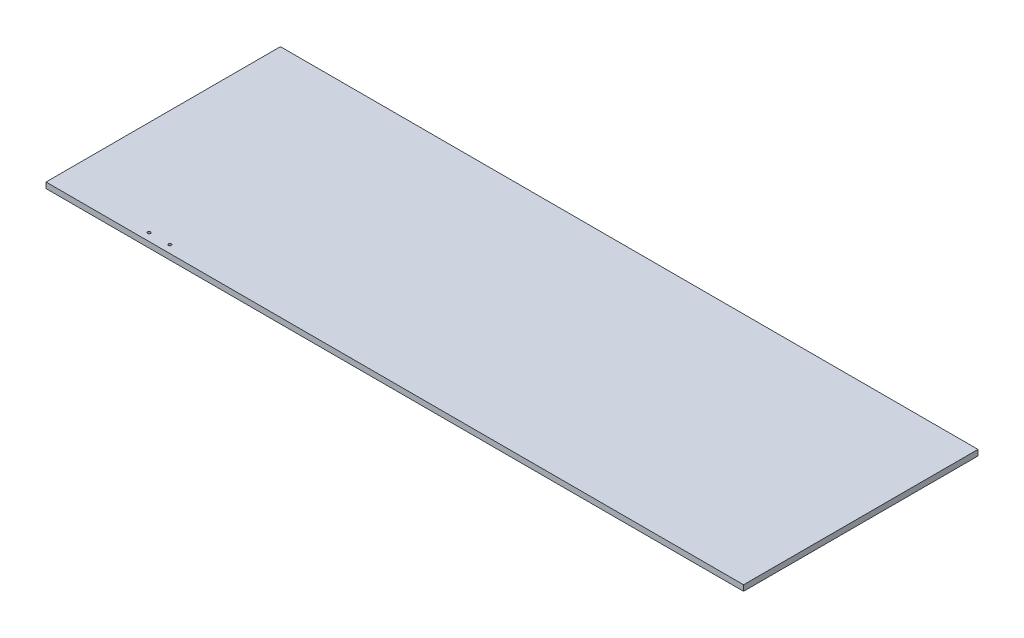
SolidWorks part; units mm, degrees
material "Oak"
ref_plane "Front Plane" through (0, 0, 0) normal (0, 0, 1) x (1, 0, 0)
ref_plane "Top Plane" through (0, 0, 0) normal (0, 1, 0) x (1, 0, 0)
ref_plane "Right Plane" through (0, 0, 0) normal (1, 0, 0) x (0, 0, -1)
sketch "Sketch1" plane through (0, 0, 0) normal (0, 1, 0) x (1, 0, 0)
  line L1 (0, 410) -> (1220, 410)
  line L2 (0, 410) -> (0, 0)
  line L3 (0, 0) -> (1220, 0)
  line L4 (1220, 410) -> (1220, 0)
  point P4 (0, 0)
  point P8 (0, 0)
extrude "Boss-Extrude1" add sketch "Sketch1" along normal blind 10 contours L2 L3 L4 L1
sketch "Sketch2" plane through (0, 0, 0) normal (0, 1, 0) x (1, 0, 0)
  circle A0 centre (166.8, 13.5) radius 2.5
  circle A1 centre (203.3, 13.5) radius 2.5
  point P2 (0, 0)
  point P5 (0, 0)
  point P6 (0, 0)
  point P7 (0, 0)
  point P8 (0, 0)
  point P9 (0, 0)
  point P10 (0, 0)
  point P11 (0, 0)
  point P12 (0, 0)
  point P13 (0, 0)
  point P14 (0, 0)
  point P15 (0, 0)
  point P16 (0, 0)
  point P17 (0, 0)
  point P18 (0, 0)
  point P19 (0, 0)
  point P20 (0, 0)
  point P21 (0, 0)
extrude "Cut-Extrude1" cut sketch "Sketch2" along normal blind 10
